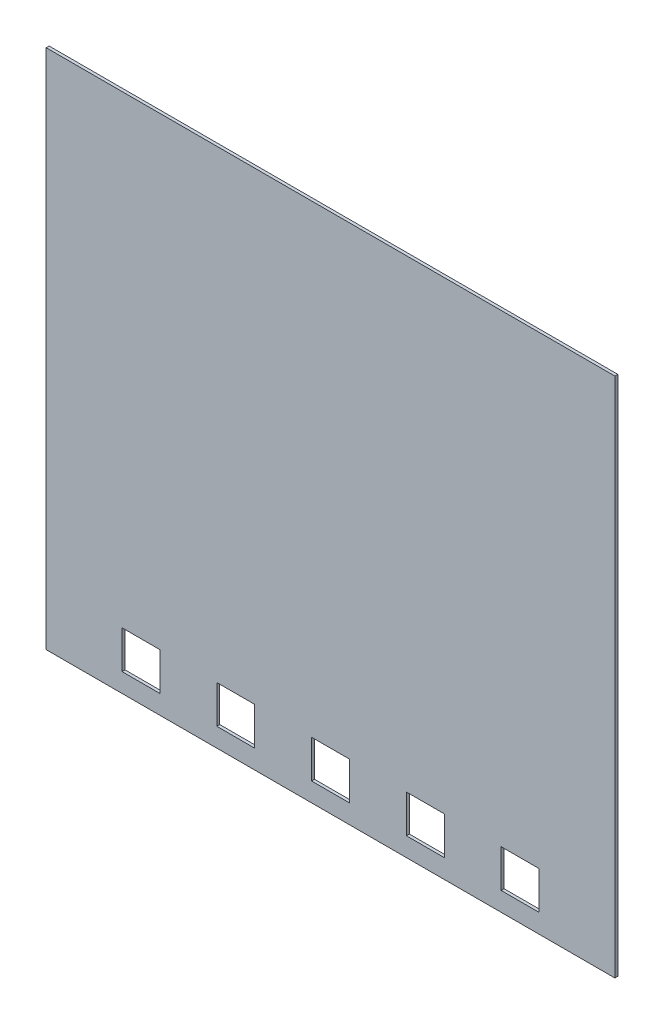
SolidWorks part; units mm, degrees
ref_plane "Front" through (0, 0, 0) normal (0, 0, 1) x (1, 0, 0)
ref_plane "Top" through (0, 0, 0) normal (0, 1, 0) x (1, 0, 0)
ref_plane "Right" through (0, 0, 0) normal (1, 0, 0) x (0, 0, -1)
sketch "Sketch1" plane through (0, 0, 0) normal (0, 0, 1) x (1, 0, 0)
  line L1 (0, 0) -> (-76.2, 0)
  line L2 (0, 0) -> (0, 69.85)
  line L3 (0, 69.85) -> (-76.2, 69.85)
  line L4 (-76.2, 0) -> (-76.2, 69.85)
  dimension "D1" = 76.2
  dimension "D2" = 69.85
extrude "Boss-Extrude1" add sketch "Sketch1" along normal blind 0.3969
sketch "Sketch2" plane through (0, 0, 0) normal (0, 0, -1) x (-1, 0, 0)
  line L0 (76.2, 0) -> (0, 0) construction
  line L1 (66.04, 2.54) -> (60.96, 2.54)
  line L2 (66.04, 2.54) -> (66.04, 7.62)
  line L3 (66.04, 7.62) -> (60.96, 7.62)
  line L4 (60.96, 2.54) -> (60.96, 7.62)
  line L5 (53.34, 2.54) -> (48.26, 2.54)
  line L6 (53.34, 2.54) -> (53.34, 7.62)
  line L7 (53.34, 7.62) -> (48.26, 7.62)
  line L8 (48.26, 2.54) -> (48.26, 7.62)
  line L9 (40.64, 2.54) -> (35.56, 2.54)
  line L10 (40.64, 2.54) -> (40.64, 7.62)
  line L11 (40.64, 7.62) -> (35.56, 7.62)
  line L12 (35.56, 2.54) -> (35.56, 7.62)
  line L13 (27.94, 2.54) -> (22.86, 2.54)
  line L14 (27.94, 2.54) -> (27.94, 7.62)
  line L15 (27.94, 7.62) -> (22.86, 7.62)
  line L16 (22.86, 2.54) -> (22.86, 7.62)
  line L17 (15.24, 2.54) -> (10.16, 2.54)
  line L18 (15.24, 2.54) -> (15.24, 7.62)
  line L19 (15.24, 7.62) -> (10.16, 7.62)
  line L20 (10.16, 2.54) -> (10.16, 7.62)
  point P20 (38.1, 2.54)
  point P21 (38.1, 0)
  dimension "D1" = 5.08
  dimension "D2" = 7.62
  dimension "D3" = 7.62
  dimension "D4" = 7.62
  dimension "D5" = 7.62
  dimension "D6" = 2.54
extrude "Cut-Extrude1" cut sketch "Sketch2" against normal through all
equation "\"D3@Sketch2\"=\"D2@Sketch2\""
equation "\"D4@Sketch2\"=\"D2@Sketch2\""
equation "\"D5@Sketch2\"=\"D2@Sketch2\""
